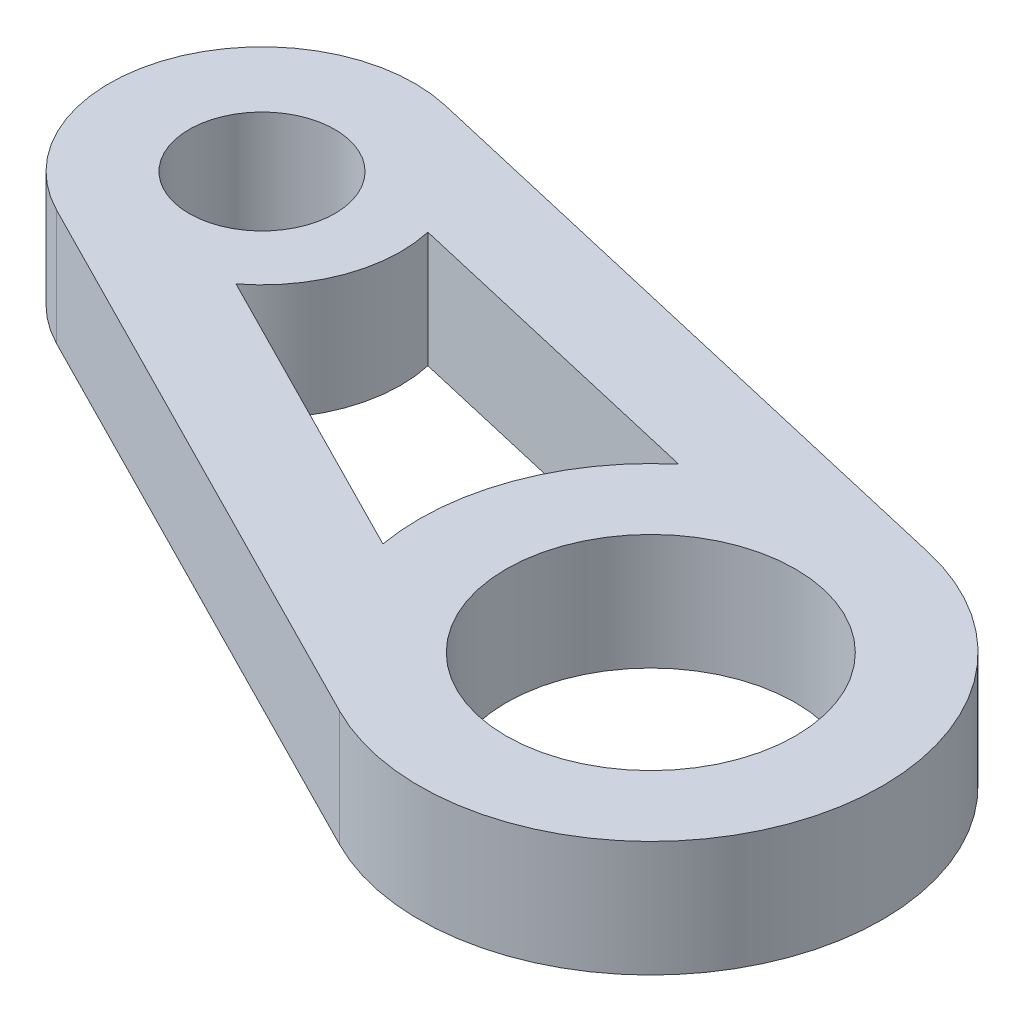
SolidWorks part; units mm, degrees
material "6061-T6 (SS)"
ref_plane "X-Y Datum" through (0, 0, 0) normal (0, 0, 1) x (1, 0, 0)
ref_plane "X-Z Datum" through (0, 0, 0) normal (0, 1, 0) x (1, 0, 0)
ref_plane "Y-Z Datum" through (0, 0, 0) normal (1, 0, 0) x (0, 0, -1)
sketch "Sketch1" plane through (0, 0, 0) normal (0, 1, 0) x (1, 0, 0)
  line L11 (16.764, -6.096) -> (0, 0) construction
  line L12 (18.1958, 0.0905) -> (0.945, 4.0831)
  line L16 (13.8876, -11.7572) -> (-1.8984, -3.7364)
  line L17 (10.5092, -7.1916) -> (2.3134, -3.0273)
  line L18 (12.6739, -1.2387) -> (3.7175, 0.8342)
  circle A8 centre (0, 0) radius 2
  circle A9 centre (16.764, -6.096) radius 3.9688
  arc A11 (18.1958, 0.0905) -> (13.8876, -11.7572) centre (16.764, -6.096) cw
  arc A15 (-1.8984, -3.7364) -> (0.945, 4.0831) centre (0, 0) cw
  arc A16 (2.3134, -3.0273) -> (3.7175, 0.8342) centre (0, 0) ccw
  arc A17 (12.6739, -1.2387) -> (10.5092, -7.1916) centre (16.764, -6.096) ccw
  dimension "D1" = 4
  dimension "D4" = 6.35
  dimension "D2" = 16.764
  dimension "D5" = 7.9375
  dimension "D3" = 6.096
  dimension "D6" = 4.191
  dimension "D7" = 6.35
  dimension "D8" = 3.81
  dimension "D9" = 2.54
  dimension "D10" = 2.54
extrude "Boss-Extrude1" add sketch "Sketch1" along normal blind 3.175
